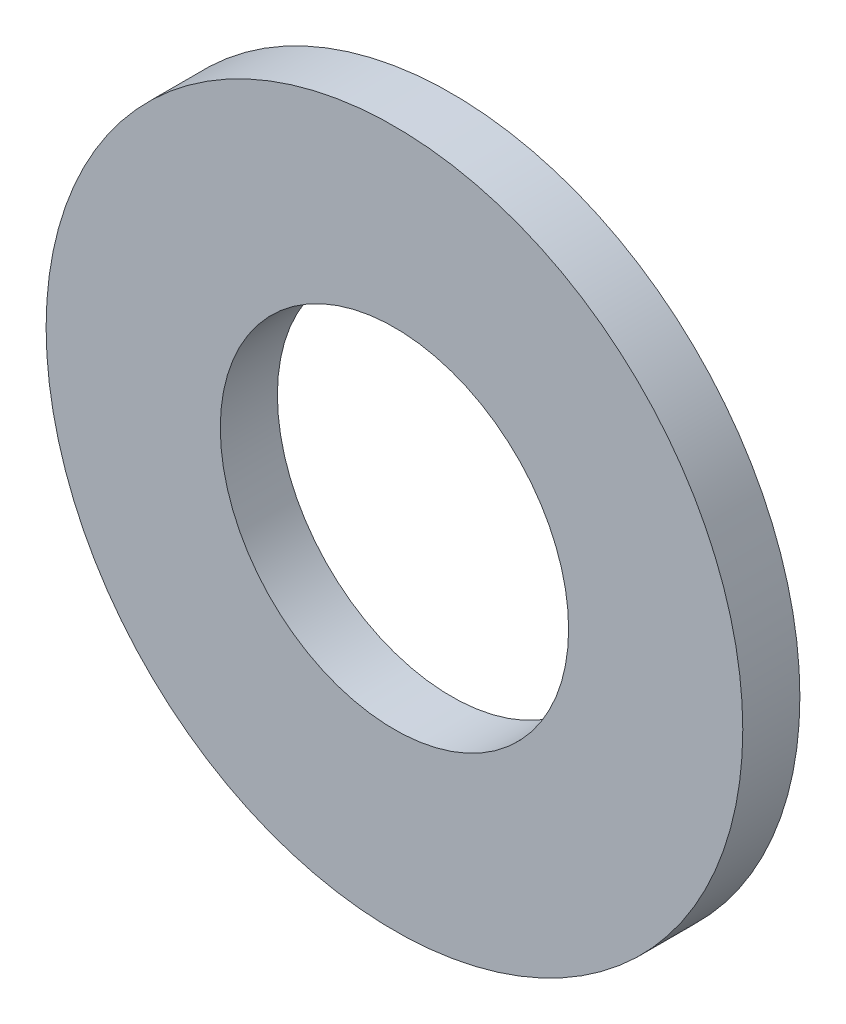
SolidWorks part; units mm, degrees
ref_plane "Front Plane" through (0, 0, 0) normal (0, 0, 1) x (1, 0, 0)
ref_plane "Top Plane" through (0, 0, 0) normal (0, 1, 0) x (1, 0, 0)
ref_plane "Right Plane" through (0, 0, 0) normal (1, 0, 0) x (0, 0, -1)
sketch "Sketch1" plane through (0, 0, 0) normal (0, 0, 1) x (1, 0, 0)
  circle A0 centre (0, 0) radius 3.05
  circle A1 centre (0, 0) radius 6.1
  dimension "D1" = 6.1
  dimension "D2" = 12.2
extrude "Boss-Extrude1" add sketch "Sketch1" along normal blind 1
